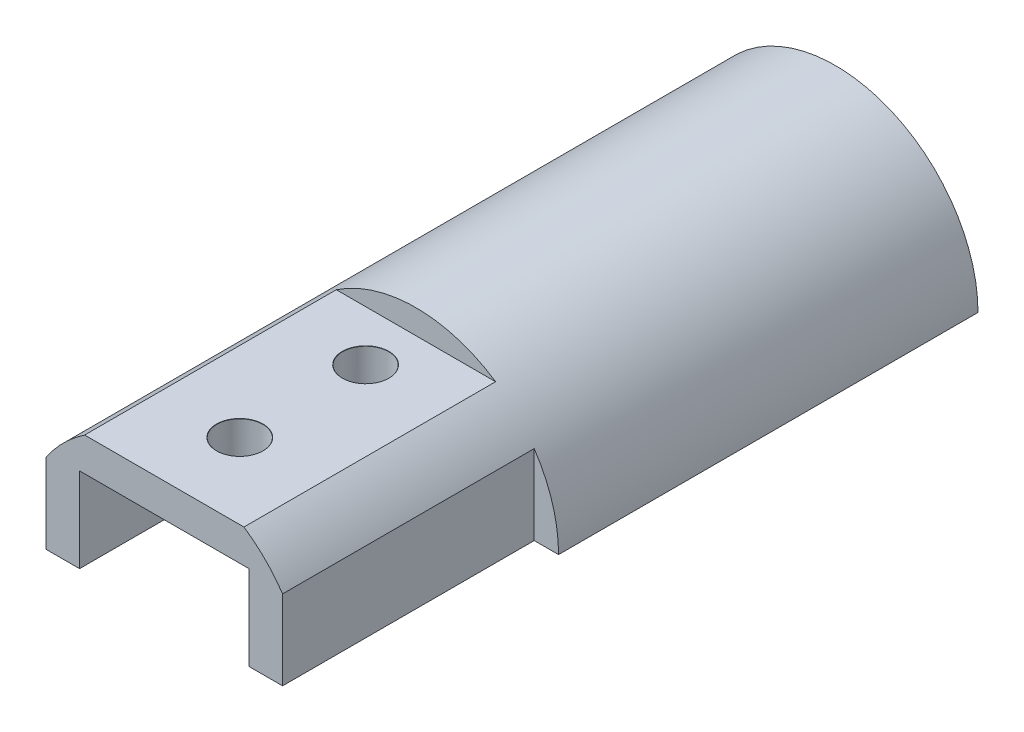
SolidWorks part; units mm, degrees
ref_plane "前视基准面" through (0, 0, 0) normal (0, 0, 1) x (1, 0, 0)
ref_plane "上视基准面" through (0, 0, 0) normal (0, 1, 0) x (1, 0, 0)
ref_plane "右视基准面" through (0, 0, 0) normal (1, 0, 0) x (0, 0, -1)
sketch "草图1" plane through (0, 0, 0) normal (0, 0, 1) x (1, 0, 0)
  circle A0 centre (0, 0) radius 17
  dimension "D1" = 34
extrude "凸台-拉伸1" add sketch "草图1" along normal blind 3
sketch "草图2" plane through (0, 0, 3) normal (0, 0, 1) x (1, 0, 0)
  circle A0 centre (0, 0) radius 17 construction
  circle A1 centre (0, 0) radius 17
  circle A2 centre (0, 0) radius 15
  dimension "D1" = 30
extrude "凸台-拉伸2" add sketch "草图2" along normal blind 40
sketch "草图3" plane through (0, 0, 3) normal (0, 0, 1) x (1, 0, 0)
  circle A0 centre (0, 0) radius 5
  dimension "D1" = 10
extrude "切除-拉伸1" cut sketch "草图3" against normal through all
sketch "草图4" plane through (0, 0, 43) normal (0, 0, 1) x (1, 0, 0)
  line L0 (0, 17) -> (0, -17) construction
  line L1 (-17, 0) -> (0, 0) construction
  line L2 (-4.4431, 10.1) -> (4.4431, 10.1)
  line L7 (10.1, 4.4431) -> (10.1, -4.4431)
  line L8 (-10.1, 4.4431) -> (-10.1, -4.4431)
  line L9 (-4.4431, 10.1) -> (-10.1, 4.4431)
  line L10 (4.4431, 10.1) -> (10.1, 4.4431)
  line L11 (-4.4431, -10.1) -> (-10.1, -4.4431)
  line L12 (-4.4431, -10.1) -> (4.4431, -10.1)
  line L13 (4.4431, -10.1) -> (10.1, -4.4431)
  circle A0 centre (0, 0) radius 17
  point P17 (0, 10.1)
  point P18 (-10.1, 0)
  point P21 (10.1, 0)
  dimension "D1" = 10.1
  dimension "D2" = 10.1
  dimension "D3" = 8
  dimension "D4" = 135
extrude "凸台-拉伸3" add sketch "草图4" along normal blind 7
sketch "草图5" plane through (0, 0, 50) normal (0, 0, 1) x (1, 0, 0)
  line L2 (-9.4968, 14.1) -> (9.4968, 14.1)
  line L4 (-14.1, 9.4968) -> (-14.1, -9.4968)
  line L6 (0, 0) -> (10.1, 10.1) construction
  line L7 (14.1, -9.4968) -> (14.1, 9.4968)
  line L8 (9.4968, -14.1) -> (-9.4968, -14.1)
  line L11 (-10.1, 10.1) -> (-10.1, -10.1)
  line L12 (-10.1, -10.1) -> (10.1, -10.1)
  line L13 (10.1, -10.1) -> (10.1, 10.1)
  line L14 (10.1, 10.1) -> (-10.1, 10.1)
  circle A1 centre (0, 0) radius 17 construction
  arc A2 (-14.1, -9.4968) -> (-9.4968, -14.1) centre (0, 0) ccw
  arc A3 (-9.4968, 14.1) -> (-14.1, 9.4968) centre (0, 0) ccw
  arc A4 (14.1404, 9.4366) -> (9.4366, 14.1404) centre (0, 0) ccw
  arc A5 (14.1, -9.4968) -> (9.4968, -14.1) centre (0, 0) cw
  dimension "D1" = 4
  dimension "D2" = 4
  dimension "D3" = 20.2
  dimension "D4" = 20.2
extrude "凸台-拉伸4" add sketch "草图5" along normal blind 30
hole_wizard "M5 间隙孔2" positions "草图6" profile "草图7" hole size "M5" standard "ISO" end condition through all
sketch "草图6" plane through (0, 14.1, 0) normal (0, 1, 0) x (1, 0, 0)
  line L2 (-9.4968, -50) -> (9.4968, -50) construction
  line L3 (0, -83) -> (0, -30.4102) construction
  point P0 (0, -56)
  point P2 (0, -71)
  dimension "D1" = 6
  dimension "D2" = 15
sketch "草图7" plane through (0, 14.1, 56) normal (1, 0, 0) x (0, 0, 1)
  line L0 (0, 0) -> (0, 31.1)
  line L1 (0, 31.1) -> (2.75, 31.1)
  line L2 (2.75, 31.1) -> (2.75, 0.025)
  line L3 (2.75, 0.025) -> (2.775, 0)
  line L5 (2.775, 0) -> (0, 0)
  line L6 (-2.75, 0.025) -> (-2.775, 0) construction
  line L11 (0, -6.35) -> (0, 107.95) construction
  dimension "通孔孔直径" = 5.5
  dimension "通孔孔深度" = 31.1
  dimension "近端锥形沉头孔直径" = 5.55
  dimension "近端锥形沉头孔角度" = 90
hole_wizard "M2.5 间隙孔2" positions "草图9" profile "草图10" hole size "M2.5" standard "ISO"
sketch "草图9" plane through (0, 0, 3) normal (0, 0, 1) x (1, 0, 0)
  point P0 (11, 0)
  point P11 (11, 0)
  point P12 (11, 0)
  point P13 (11, 0)
  point P20 (11, 0)
  point P21 (11, 0)
  point P22 (11, 0)
  point P31 (7.7782, -7.7782)
  point P32 (0, -11)
  point P33 (-7.7782, -7.7782)
  point P34 (-11, 0)
  point P35 (-7.7782, 7.7782)
  point P36 (0, 11)
  point P37 (7.7782, 7.7782)
  dimension "D1" = 11
  dimension "D2" = 4
  dimension "D3" = 4
  dimension "D4" = 8
sketch "草图10" plane through (11, 0, 3) normal (1, 0, 0) x (0, -1, 0)
  line L0 (0, 0) -> (0, 3)
  line L1 (0, 3) -> (1.45, 3)
  line L2 (1.45, 3) -> (1.45, 0.025)
  line L3 (1.45, 0.025) -> (1.475, 0)
  line L5 (1.475, 0) -> (0, 0)
  line L6 (-1.45, 0.025) -> (-1.475, 0) construction
  line L11 (0, -6.35) -> (0, 107.95) construction
  dimension "通孔孔直径" = 2.9
  dimension "通孔孔深度" = 3
  dimension "近端锥形沉头孔直径" = 2.95
  dimension "近端锥形沉头孔角度" = 90
sketch "草图12" plane through (0, 0, 0) normal (0, 1, 0) x (1, 0, 0)
  line L1 (22.8146, 3.072) -> (-24.3727, 3.072)
  line L2 (22.8146, 3.072) -> (22.8146, -86.2946)
  line L3 (22.8146, -86.2946) -> (-24.3727, -86.2946)
  line L4 (-24.3727, 3.072) -> (-24.3727, -86.2946)
extrude "切除-拉伸2" cut sketch "草图12" against normal blind 18
